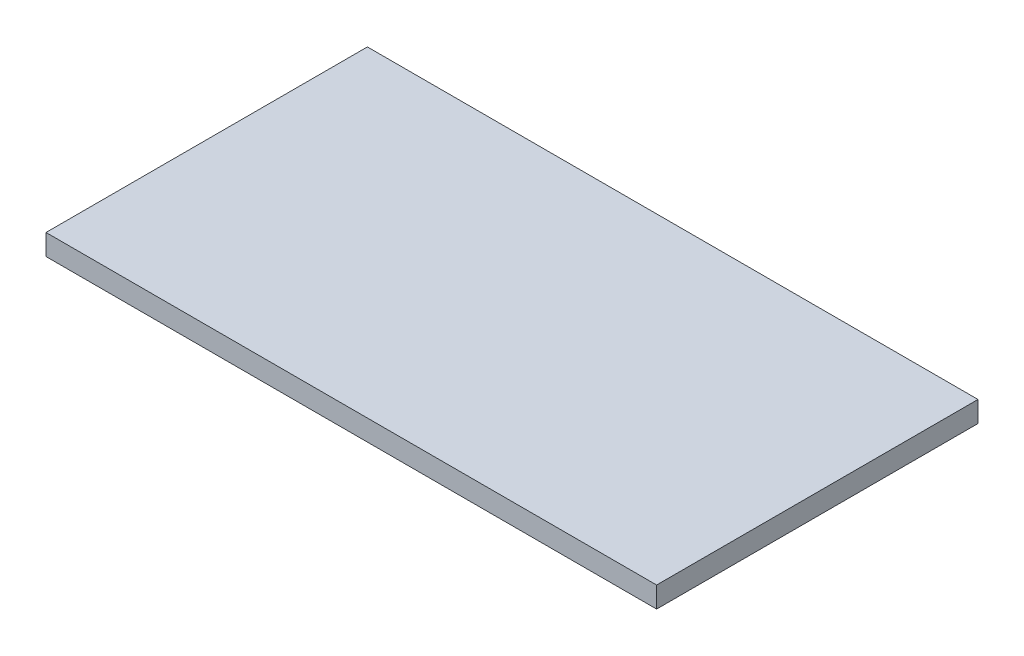
SolidWorks part; units mm, degrees
ref_plane "Front Plane" through (0, 0, 0) normal (0, 0, 1) x (1, 0, 0)
ref_plane "Top Plane" through (0, 0, 0) normal (0, 1, 0) x (1, 0, 0)
ref_plane "Right Plane" through (0, 0, 0) normal (1, 0, 0) x (0, 0, -1)
sketch "Sketch1" plane through (0, 0, 0) normal (0, 1, 0) x (1, 0, 0)
  line L1 (-101.6505, 10.5328) -> (84.2033, 10.5328)
  line L2 (-101.6505, 10.5328) -> (-101.6505, -87.2894)
  line L3 (-101.6505, -87.2894) -> (84.2033, -87.2894)
  line L4 (84.2033, 10.5328) -> (84.2033, -87.2894)
extrude "Boss-Extrude1" add sketch "Sketch1" along normal blind 6.35
